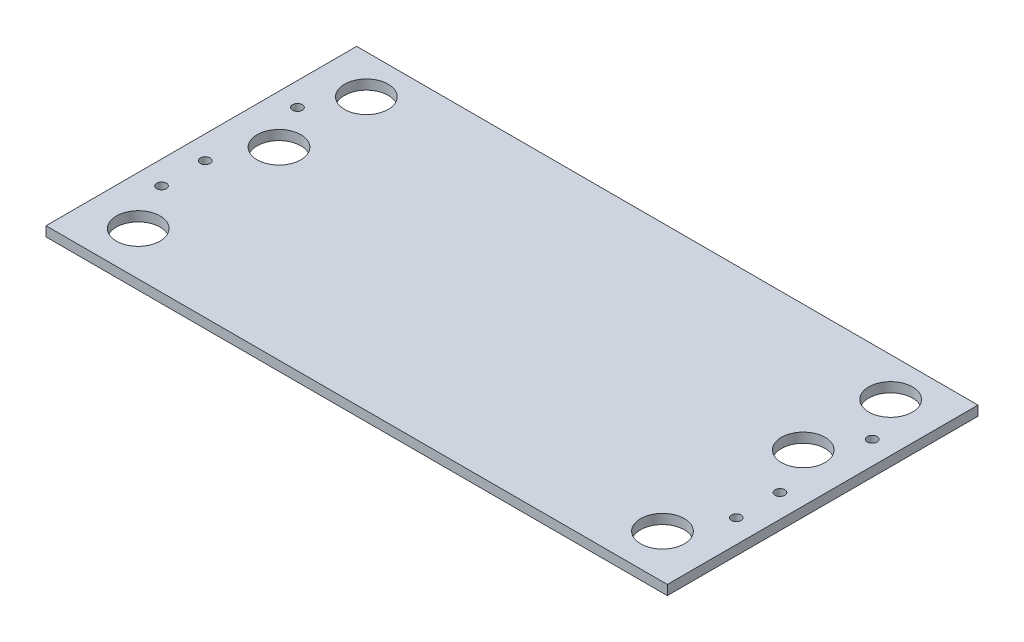
SolidWorks part; units mm, degrees
ref_plane "Front Plane" through (0, 0, 0) normal (0, 0, 1) x (1, 0, 0)
ref_plane "Top Plane" through (0, 0, 0) normal (0, 1, 0) x (1, 0, 0)
ref_plane "Right Plane" through (0, 0, 0) normal (1, 0, 0) x (0, 0, -1)
sketch "Sketch2" plane through (0, 0, 0) normal (0, 1, 0) x (1, 0, 0)
  line L0 (-203.2, -101.6) -> (-203.2, 101.6)
  line L1 (-203.2, 101.6) -> (203.2, 101.6)
  line L2 (203.2, 101.6) -> (203.2, -101.6)
  line L3 (203.2, -101.6) -> (-203.2, -101.6)
  line L4 (0, -55) -> (0, 55) construction
  circle A0 centre (-171.45, 76.2) radius 14.2875
  circle A1 centre (-171.45, 19.05) radius 14.2875
  circle A2 centre (171.45, 76.2) radius 14.2875
  circle A3 centre (171.45, 19.05) radius 14.2875
  circle A4 centre (171.45, -73.025) radius 14.2875
  circle A5 centre (-171.45, -73.025) radius 14.2875
  circle A6 centre (-187.96, -12.7) radius 3.175
  circle A7 centre (-187.96, -41.275) radius 3.175
  circle A8 centre (187.96, -41.275) radius 3.175
  circle A9 centre (187.96, -12.7) radius 3.175
  circle A10 centre (-187.96, 47.625) radius 3.175
  circle A11 centre (187.96, 47.625) radius 3.175
  dimension "D5" = 28.575
  dimension "D7" = 57.15
  dimension "D14" = 31.75
  dimension "D16" = 6.35
  dimension "D18" = 6.35
  dimension "D1" = 203.2
  dimension "D2" = 406.4
  dimension "D3" = 203.2
  dimension "D4" = 101.6
  dimension "D6" = 57.15
  dimension "D8" = 25.4
  dimension "D9" = 25.4
  dimension "D10" = 149.225
  dimension "D11" = 149.225
  dimension "D12" = 31.75
  dimension "D13" = 31.75
  dimension "D15" = 31.75
  dimension "D17" = 15.24
  dimension "D19" = 28.575
extrude "Boss-Extrude1" add sketch "Sketch2" along normal blind 6.35
